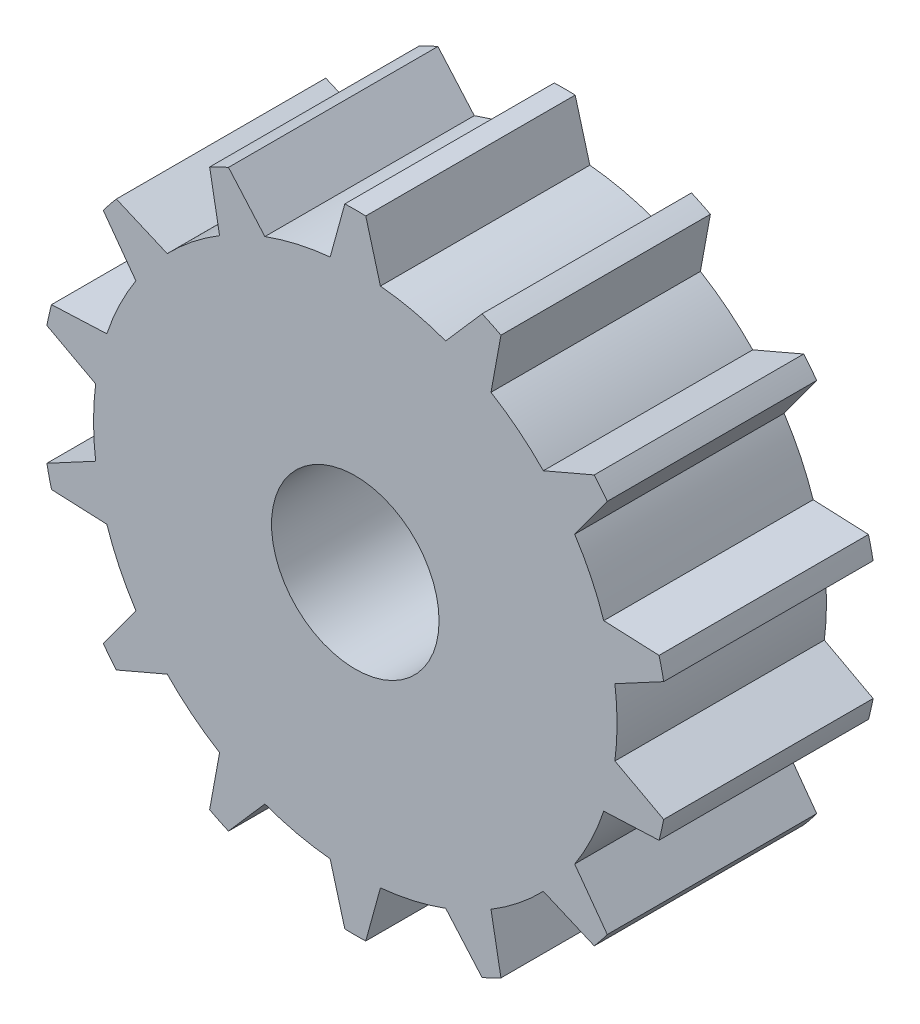
SolidWorks part; units mm, degrees
ref_plane "Plan de face" through (0, 0, 0) normal (0, 0, 1) x (1, 0, 0)
ref_plane "Plan de dessus" through (0, 0, 0) normal (0, 1, 0) x (1, 0, 0)
ref_plane "Plan de droite" through (0, 0, 0) normal (1, 0, 0) x (0, 0, -1)
sketch "Esquisse2" plane through (0, 0, 0) normal (0, 0, 1) x (1, 0, 0)
  line L0 (-20.4999, 14.9917) -> (-21.2, 12.4423)
  line L1 (-20, 0) -> (-20, 21.5813) construction
  line L2 (-19.5001, 14.9917) -> (-18.8, 12.4423)
  line L3 (-13.9458, 13.7239) -> (-15.6827, 11.7308)
  line L4 (-13.0449, 13.2901) -> (-13.5203, 10.6894)
  line L5 (-8.5907, 9.738) -> (-11.0204, 8.6958)
  line L6 (-7.9673, 8.9563) -> (-9.5241, 6.8194)
  line L7 (-5.4955, 3.8234) -> (-8.1367, 3.9386)
  line L8 (-5.273, 2.8486) -> (-7.6027, 1.5988)
  line L9 (-5.273, -2.8486) -> (-7.6027, -1.5988)
  line L10 (-5.4955, -3.8234) -> (-8.1367, -3.9386)
  line L11 (-7.9673, -8.9563) -> (-9.5241, -6.8194)
  line L12 (-8.5907, -9.738) -> (-11.0204, -8.6958)
  line L13 (-13.0449, -13.2901) -> (-13.5203, -10.6894)
  line L14 (-13.9458, -13.7239) -> (-15.6827, -11.7308)
  line L15 (-19.5001, -14.9917) -> (-18.8, -12.4423)
  line L16 (-20.4999, -14.9917) -> (-21.2, -12.4423)
  line L17 (-26.0542, -13.7239) -> (-24.3173, -11.7308)
  line L18 (-26.9551, -13.2901) -> (-26.4797, -10.6894)
  line L19 (-31.4093, -9.738) -> (-28.9796, -8.6958)
  line L20 (-32.0327, -8.9563) -> (-30.4759, -6.8194)
  line L45 (-34.5045, -3.8234) -> (-31.8633, -3.9386)
  line L46 (-34.727, -2.8486) -> (-32.3973, -1.5988)
  line L47 (-34.727, 2.8486) -> (-32.3973, 1.5988)
  line L48 (-34.5045, 3.8234) -> (-31.8633, 3.9386)
  line L49 (-32.0327, 8.9563) -> (-30.4759, 6.8194)
  line L50 (-31.4093, 9.738) -> (-28.9796, 8.6958)
  line L51 (-26.9551, 13.2901) -> (-26.4797, 10.6894)
  line L52 (-26.0542, 13.7239) -> (-24.3173, 11.7308)
  arc A0 (-19.5001, 14.9917) -> (-20.4999, 14.9917) centre (-20, 0) ccw
  arc A1 (-18.8, 12.4423) -> (-21.2, 12.4423) centre (-20, 0) ccw
  arc A2 (-13.5203, 10.6894) -> (-15.6827, 11.7308) centre (-20, 0) ccw
  arc A3 (-13.0449, 13.2901) -> (-13.9458, 13.7239) centre (-20, 0) ccw
  arc A4 (-9.5241, 6.8194) -> (-11.0204, 8.6958) centre (-20, 0) ccw
  arc A5 (-7.9673, 8.9563) -> (-8.5907, 9.738) centre (-20, 0) ccw
  arc A6 (-7.6027, 1.5988) -> (-8.1367, 3.9386) centre (-20, 0) ccw
  arc A7 (-5.273, 2.8486) -> (-5.4955, 3.8234) centre (-20, 0) ccw
  arc A8 (-8.1367, -3.9386) -> (-7.6027, -1.5988) centre (-20, 0) ccw
  arc A9 (-5.4955, -3.8234) -> (-5.273, -2.8486) centre (-20, 0) ccw
  arc A10 (-11.0204, -8.6958) -> (-9.5241, -6.8194) centre (-20, 0) ccw
  arc A11 (-8.5907, -9.738) -> (-7.9673, -8.9563) centre (-20, 0) ccw
  arc A12 (-15.6827, -11.7308) -> (-13.5203, -10.6894) centre (-20, 0) ccw
  arc A13 (-13.9458, -13.7239) -> (-13.0449, -13.2901) centre (-20, 0) ccw
  arc A14 (-21.2, -12.4423) -> (-18.8, -12.4423) centre (-20, 0) ccw
  arc A15 (-20.4999, -14.9917) -> (-19.5001, -14.9917) centre (-20, 0) ccw
  arc A16 (-26.4797, -10.6894) -> (-24.3173, -11.7308) centre (-20, 0) ccw
  arc A17 (-26.9551, -13.2901) -> (-26.0542, -13.7239) centre (-20, 0) ccw
  arc A18 (-30.4759, -6.8194) -> (-28.9796, -8.6958) centre (-20, 0) ccw
  arc A19 (-32.0327, -8.9563) -> (-31.4093, -9.738) centre (-20, 0) ccw
  arc A44 (-32.3973, -1.5988) -> (-31.8633, -3.9386) centre (-20, 0) ccw
  arc A45 (-34.727, -2.8486) -> (-34.5045, -3.8234) centre (-20, 0) ccw
  arc A46 (-31.8633, 3.9386) -> (-32.3973, 1.5988) centre (-20, 0) ccw
  arc A47 (-34.5045, 3.8234) -> (-34.727, 2.8486) centre (-20, 0) ccw
  arc A48 (-28.9796, 8.6958) -> (-30.4759, 6.8194) centre (-20, 0) ccw
  arc A49 (-31.4093, 9.738) -> (-32.0327, 8.9563) centre (-20, 0) ccw
  arc A50 (-24.3173, 11.7308) -> (-26.4797, 10.6894) centre (-20, 0) ccw
  arc A51 (-26.0542, 13.7239) -> (-26.9551, 13.2901) centre (-20, 0) ccw
  circle A52 centre (-20, 0) radius 12.5
  circle A53 centre (-20, 0) radius 4
  point P6 (-20, 15)
  point P8 (-20, 12.5)
  point P96 (-20, 0)
  dimension "D1" = 30
  dimension "D2" = 25
  dimension "D6" = 8
  dimension "D3" = 0.5
  dimension "D4" = 1.2
  dimension "D5" = 14
extrude "Boss.-Extru.1" add sketch "Esquisse2" along normal blind 10
